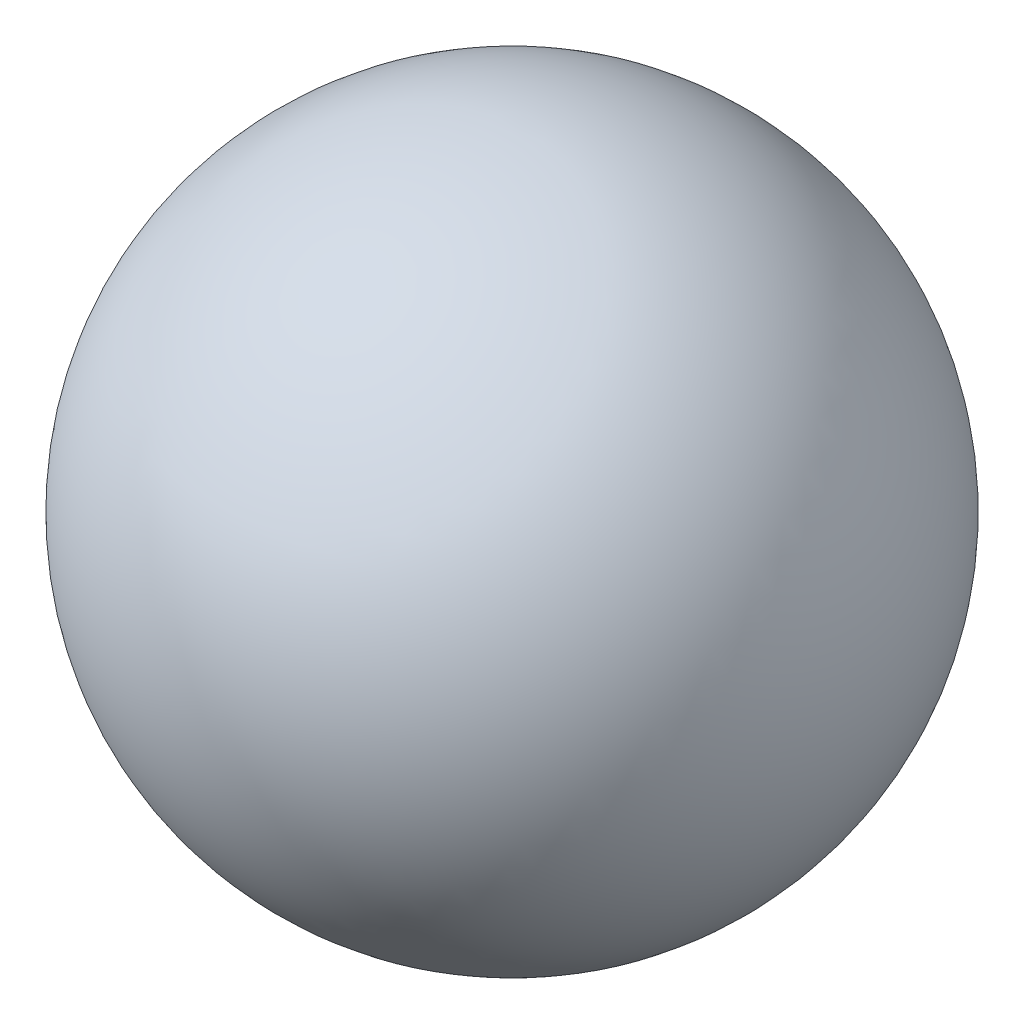
SolidWorks part; units mm, degrees
ref_plane "Front Plane" through (0, 0, 0) normal (0, 0, 1) x (1, 0, 0)
ref_plane "Top Plane" through (0, 0, 0) normal (0, 1, 0) x (1, 0, 0)
ref_plane "Right Plane" through (0, 0, 0) normal (1, 0, 0) x (0, 0, -1)
sketch "Sketch1" plane through (0, 0, 0) normal (0, 0, 1) x (1, 0, 0)
  line L0 (0, 3.95) -> (0, -3.95)
  arc A0 (0, -3.95) -> (0, 3.95) centre (0, 0) ccw
  dimension "D1" = 7.9
revolve "Revolve1" add sketch "Sketch1" angle 360 about L0
